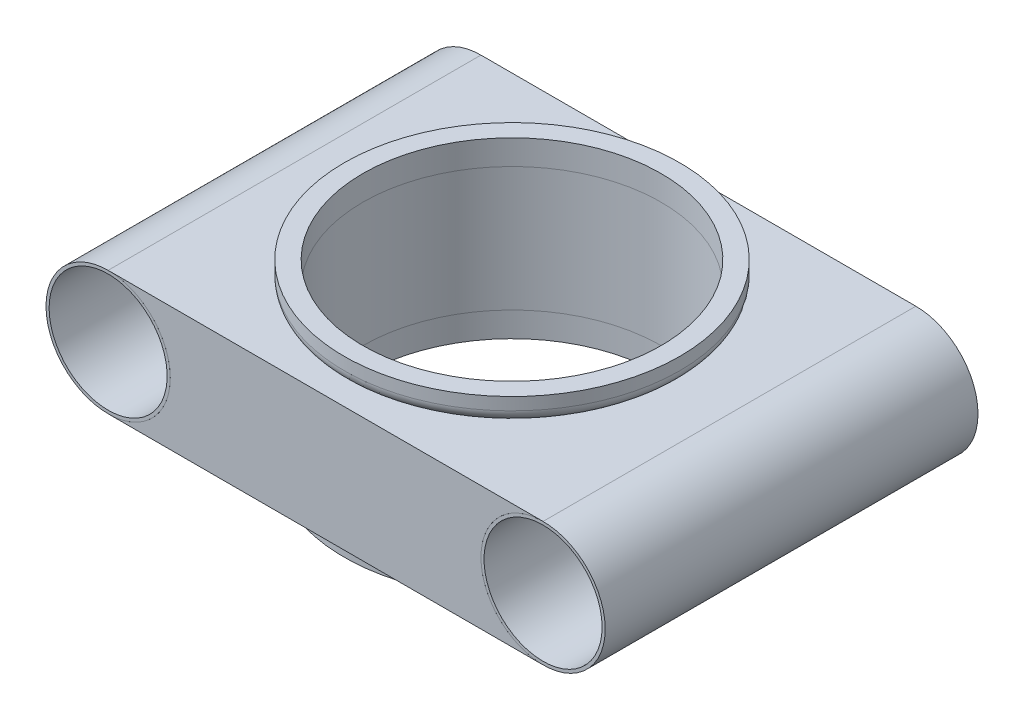
SolidWorks part; units mm, degrees
material "AISI 1020"
ref_plane "Front Plane" through (0, 0, 0) normal (0, 0, 1) x (1, 0, 0)
ref_plane "Top Plane" through (0, 0, 0) normal (0, 1, 0) x (1, 0, 0)
ref_plane "Right Plane" through (0, 0, 0) normal (1, 0, 0) x (0, 0, -1)
sketch "Sketch3" plane through (0, 0, 0) normal (0, 1, 0) x (1, 0, 0)
  line L0 (-17.5, 15) -> (-17.5, -15)
  line L1 (17.5, 15) -> (17.5, -15)
  line L2 (-17.5, 0) -> (17.5, 0) construction
  line L3 (17.5, -15) -> (-17.5, -15) construction
  line L4 (-17.5, 15) -> (17.5, 15) construction
  dimension "D1" = 35
  dimension "D2" = 30
  dimension "D3" = 17.5
other "Structural Member1"
ref_plane "Plane2" through (-17.5, 0, -15) normal (0, 0, 1) x (1, 0, 0)
sketch "Sketch1" plane through (-17.5, 0, -15) normal (0, 0, 1) x (1, 0, 0)
  circle A0 centre (0, 0) radius 5
  circle A1 centre (0, 0) radius 4.75
  point P4 (0, 0)
  dimension "D1" = 10
  dimension "D2" = 9.5
sketch "Sketch4" plane through (0, 0, 0) normal (0, 0, 1) x (1, 0, 0)
  line L0 (-17.5, 5) -> (17.5, 5)
  line L1 (17.5, -5) -> (-17.5, -5)
  arc A0 (17.5, -5) -> (17.5, 5) centre (17.5, 0) ccw
  arc A1 (-17.5, 5) -> (-17.5, -5) centre (-17.5, 0) ccw
  circle A2 centre (-17.5, 0) radius 5
  circle A3 centre (17.5, 0) radius 5
  arc A4 (-17.5, 5.1) -> (-17.5, -5.1) centre (-17.5, 0) ccw
  dimension "D1" = 10
  dimension "D2" = 0.1
extrude "Boss-Extrude2" add sketch "Sketch4" along normal mid plane 30 separate body contours A3 L0 A2 L1
sketch "Sketch21" plane through (0, 5, 0) normal (0, 1, 0) x (1, 0, 0)
  circle A0 centre (0, 0) radius 12
  dimension "D1" = 24
extrude "Cut-Extrude6" cut sketch "Sketch21" against normal mid plane 20 contours A0
sketch "Sketch22" plane through (0, 5, 0) normal (0, 1, 0) x (1, 0, 0)
  circle A1 centre (0, 0) radius 12
  circle A2 centre (0, 0) radius 13.5
  circle A3 centre (0, 0) radius 13.5
  dimension "D2" = 24
  dimension "D1" = 1.5
extrude "Boss-Extrude3" add sketch "Sketch22" along normal blind 2 separate body
fillet "Fillet2" radius 1 1 edges at (-13.5, 5, 0)
mirror "Mirror1" about plane through (0, 0, 0) normal (0, 1, 0) of bodies 119
